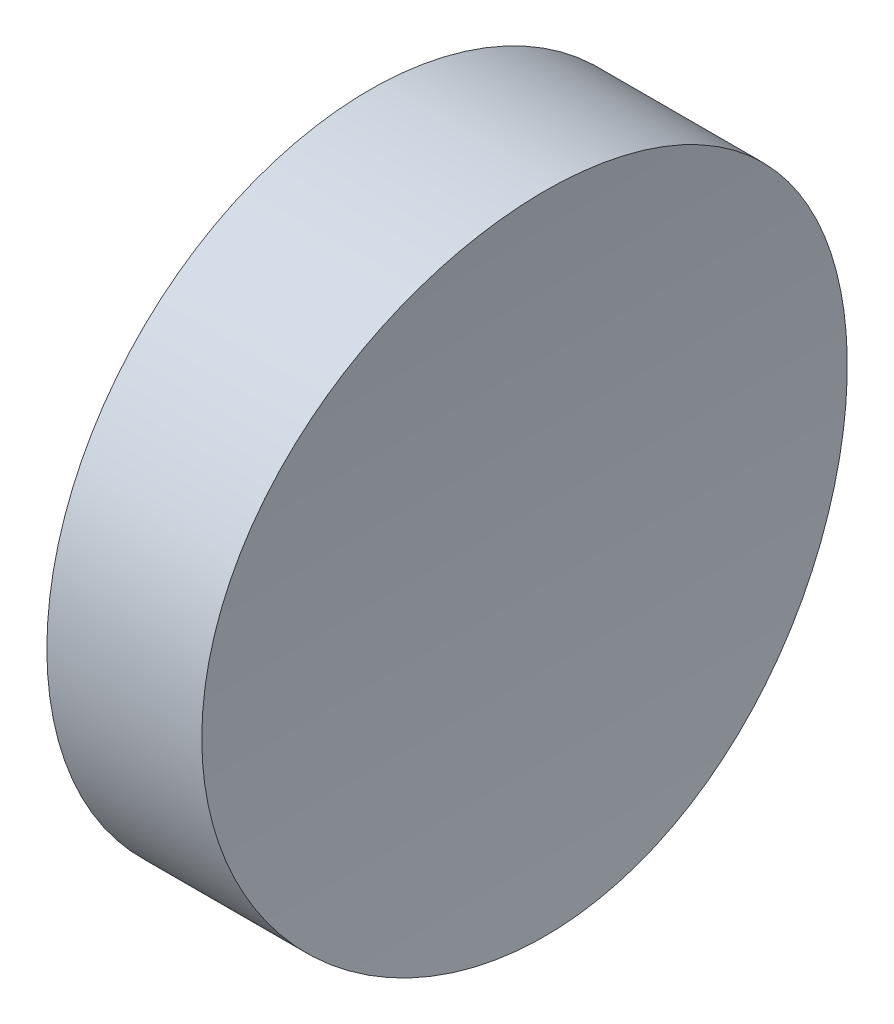
SolidWorks part; units mm, degrees
ref_plane "前视基准面" through (0, 0, 0) normal (0, 0, 1) x (1, 0, 0)
ref_plane "上视基准面" through (0, 0, 0) normal (0, 1, 0) x (1, 0, 0)
ref_plane "右视基准面" through (0, 0, 0) normal (1, 0, 0) x (0, 0, -1)
sketch "草图1" plane through (0, 0, 0) normal (1, 0, 0) x (0, 0, -1)
  circle A0 centre (0, 0) radius 12.5
  dimension "D1" = 25
extrude "凸台-拉伸1" add sketch "草图1" along normal blind 10
sketch "草图2" plane through (0, 0, 0) normal (0, 0, 1) x (1, 0, 0)
  line L0 (0, 0) -> (106, 0) construction
  line L1 (0, 0) -> (6, 0) construction
  circle A0 centre (106, 0) radius 100
  dimension "D1" = 200
  dimension "D2" = 6
extrude "切除-拉伸1" cut sketch "草图2" against normal through all both and the other way through all
